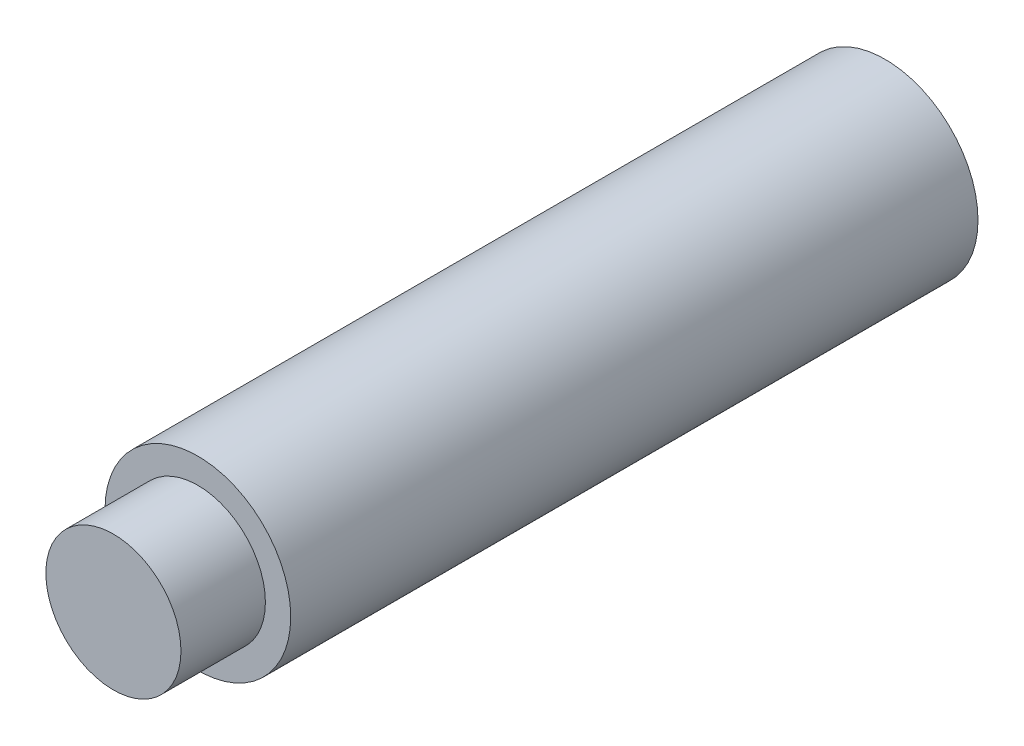
SolidWorks part; units mm, degrees
ref_plane "Front Plane" through (0, 0, 0) normal (0, 0, 1) x (1, 0, 0)
ref_plane "Top Plane" through (0, 0, 0) normal (0, 1, 0) x (1, 0, 0)
ref_plane "Right Plane" through (0, 0, 0) normal (1, 0, 0) x (0, 0, -1)
sketch "Sketch2" plane through (0, 0, 0) normal (1, 0, 0) x (0, 0, -1)
  line L0 (0, 0) -> (45.7, 0)
  line L1 (45.7, 0) -> (45.7, 5.5)
  line L2 (45.7, 5.5) -> (5, 5.5)
  line L3 (5, 5.5) -> (5, 4)
  line L4 (5, 4) -> (0, 4)
  line L5 (0, 4) -> (0, 0)
  dimension "D1" = 45.7
  dimension "D2" = 4
  dimension "D3" = 5.5
  dimension "D4" = 5
revolve "Revolve1" add sketch "Sketch2" angle 360 about L0
hole_wizard "Tap Drill for M6x1.0 Tap1" positions "Sketch4" profile "Sketch3" hole size "M6x1.0" standard "ANSI Metric"
sketch "Sketch4" plane through (0, 0, -45.7) normal (0, 0, -1) x (-1, 0, 0)
  point P0 (0, 0)
sketch "Sketch3" plane through (0, 0, -45.7) normal (1, 0, 0) x (0, 1, 0)
  line L0 (0, 0) -> (0, 8.5022)
  line L1 (0, 8.5022) -> (2.5, 7)
  line L2 (2.5, 7) -> (2.5, 0)
  line L5 (2.5, 0) -> (0, 0)
  line L10 (0, 8.5022) -> (-2.5, 7) construction
  line L11 (0, -6.35) -> (0, 107.95) construction
  dimension "Hole Dia." = 5
  dimension "Hole Depth" = 7
  dimension "Drill Angle" = 118
